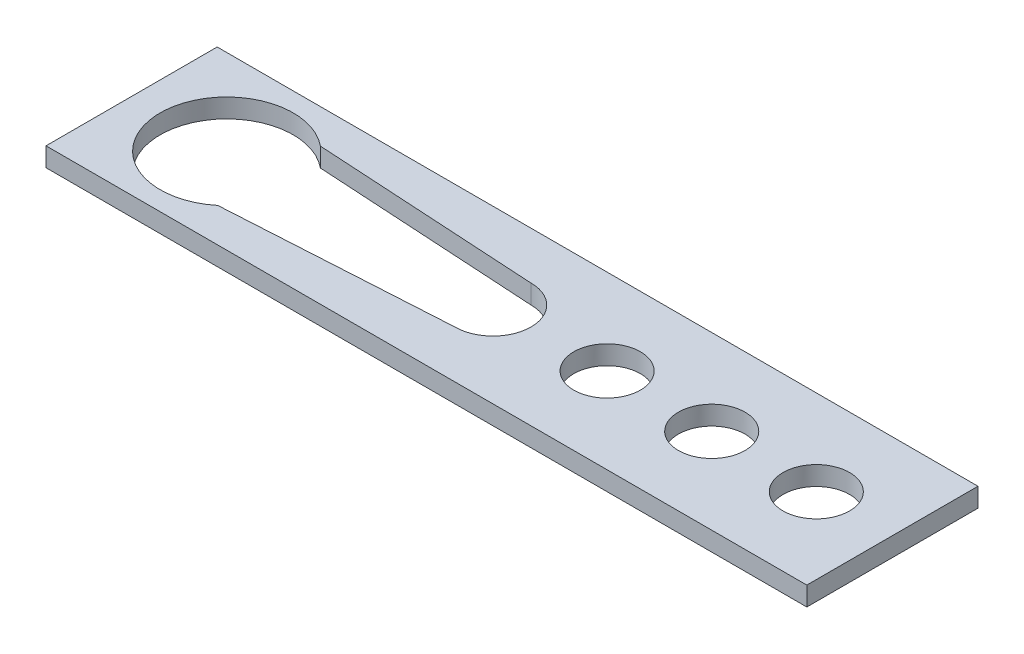
SolidWorks part; units mm, degrees
ref_plane "Front Plane" through (0, 0, 0) normal (0, 0, 1) x (1, 0, 0)
ref_plane "Top Plane" through (0, 0, 0) normal (0, 1, 0) x (1, 0, 0)
ref_plane "Right Plane" through (0, 0, 0) normal (1, 0, 0) x (0, 0, -1)
sketch "Sketch2" plane through (0, 0, 0) normal (0, 1, 0) x (1, 0, 0)
  line L1 (-20, -4.5) -> (20, -4.5)
  line L2 (-20, -4.5) -> (-20, 4.5)
  line L3 (-20, 4.5) -> (20, 4.5)
  line L4 (20, -4.5) -> (20, 4.5)
  line L5 (0, 4.5) -> (0, -4.5) construction
  line L6 (-20, 0) -> (20, 0) construction
  point P0 (0, 0)
  dimension "D1" = 9
  dimension "D2" = 40
extrude "Boss-Extrude1" add sketch "Sketch2" along normal blind 1
sketch "Sketch3" plane through (0, 1, 0) normal (0, 1, 0) x (1, 0, 0)
  line L0 (-20, 4.5) -> (-20, -4.5) construction
  line L1 (-1, 2) -> (-12.7729, 2.7)
  line L2 (-12.7729, 2.7) -> (-12.7729, -2.7)
  line L3 (-12.7729, -2.7) -> (-1, -2)
  line L4 (-20, 0) -> (20, 0) construction
  line L5 (20, -4.5) -> (20, 4.5) construction
  circle A0 centre (-15, 0) radius 3.5
  circle A1 centre (-1, 0) radius 2
  dimension "D1" = 7
  dimension "D2" = 5
  dimension "D3" = 4
  dimension "D4" = 14
  dimension "D5" = 5.4
extrude "Cut-Extrude1" cut sketch "Sketch3" against normal blind 3 contours L4 A0 L2 | A0 L4 L2 | L2 L4 A0 | L4 L2 A0 | L4 A0 L3 A1 | A0 L4 A1 L1 | A1 L4 | L4 A1
sketch "Sketch4" plane through (0, 1, 0) normal (0, 1, 0) x (1, 0, 0)
  line L0 (-20, 0) -> (20, 0) construction
  line L1 (-20, 4.5) -> (-20, -4.5) construction
  line L2 (20, -4.5) -> (20, 4.5) construction
  circle A0 centre (5, 0) radius 1.75
  arc A1 (-12.7729, 2.7) -> (-12.7729, -2.7) centre (-15, 0) ccw construction
  dimension "D1" = 3.5
  dimension "D2" = 20
extrude "Cut-Extrude2" cut sketch "Sketch4" against normal blind 3
pattern_linear "LPattern1" count 3 spacing 5.5 along (1, 0, 0) of "Cut-Extrude2"
